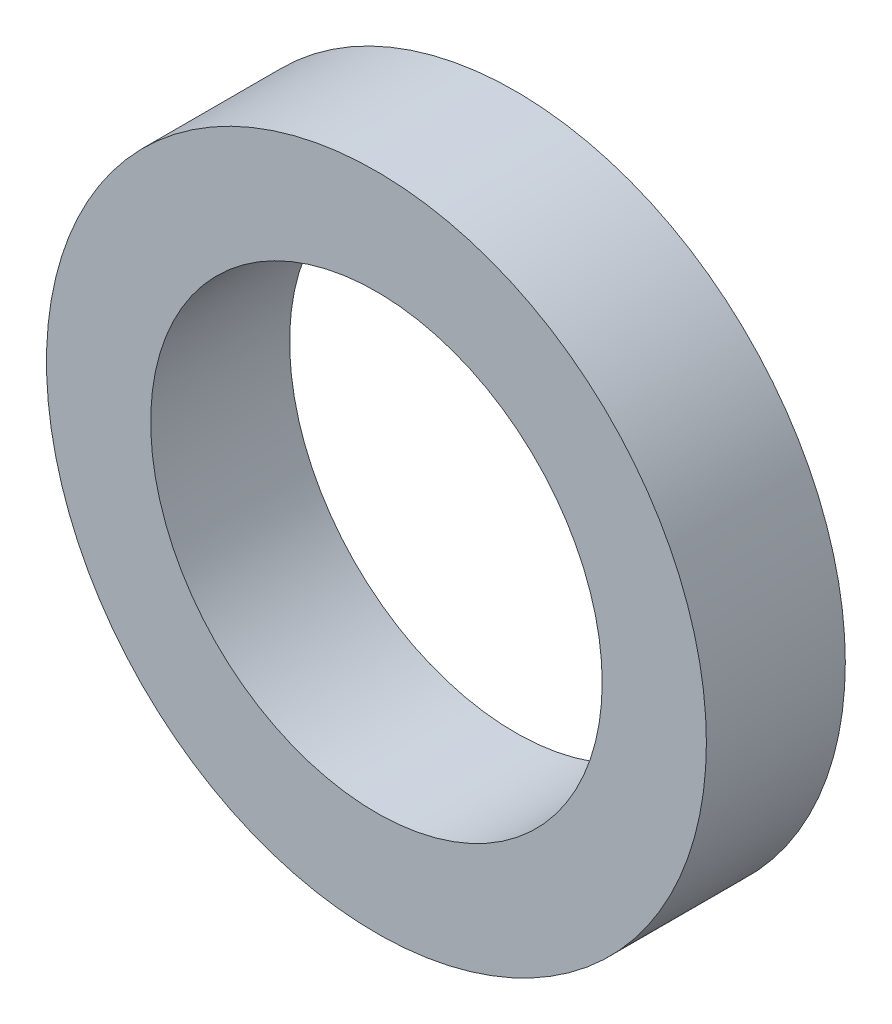
SolidWorks part; units mm, degrees
material "Alloy Steel"
ref_plane "Front Plane" through (0, 0, 0) normal (0, 0, 1) x (1, 0, 0)
ref_plane "Top Plane" through (0, 0, 0) normal (0, 1, 0) x (1, 0, 0)
ref_plane "Right Plane" through (0, 0, 0) normal (1, 0, 0) x (0, 0, -1)
sketch "Sketch1" plane through (0, 0, 0) normal (0, 0, 1) x (1, 0, 0)
  circle A0 centre (0, 0) radius 9.5
  circle A1 centre (0, 0) radius 6.5
  dimension "D1" = 13
  dimension "D2" = 19
extrude "Boss-Extrude1" add sketch "Sketch1" along normal blind 4
